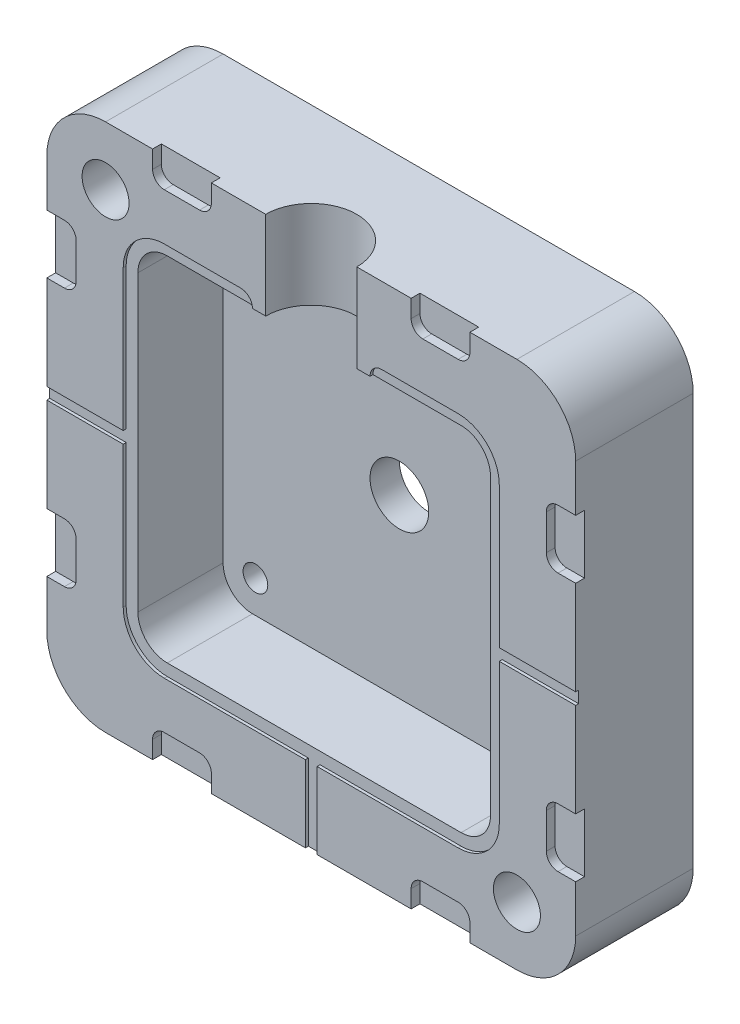
SolidWorks part; units mm, degrees
material "Alliage 1060"
ref_plane "Plan de face" through (0, 0, 0) normal (0, 0, 1) x (1, 0, 0)
ref_plane "Plan de dessus" through (0, 0, 0) normal (0, 1, 0) x (1, 0, 0)
ref_plane "Plan de droite" through (0, 0, 0) normal (1, 0, 0) x (0, 0, -1)
sketch "Esquisse1" plane through (0, 0, 0) normal (0, 0, 1) x (1, 0, 0)
  line L1 (-45, -45) -> (45, -45)
  line L2 (-45, -45) -> (-45, 45)
  line L3 (-45, 45) -> (45, 45)
  line L4 (45, -45) -> (45, 45)
  line L5 (-45, -45) -> (45, 45) construction
  line L6 (-45, 45) -> (45, -45) construction
  point P0 (0, 0)
  dimension "D1" = 90
  dimension "D2" = 90
extrude "Boss.-Extru.1" add sketch "Esquisse1" along normal blind 20
sketch "Esquisse2" plane through (0, 0, 20) normal (0, 0, 1) x (1, 0, 0)
  line L1 (-25, -30) -> (25, -30)
  line L2 (-30, -25) -> (-30, 25)
  line L3 (-25, 30) -> (25, 30)
  line L4 (30, -25) -> (30, 25)
  line L5 (-30, -30) -> (30, 30) construction
  line L6 (-30, 30) -> (30, -30) construction
  arc A0 (-25, -30) -> (-30, -25) centre (-25, -25) cw
  arc A1 (25, -30) -> (30, -25) centre (25, -25) ccw
  arc A2 (25, 30) -> (30, 25) centre (25, 25) cw
  arc A3 (-30, 25) -> (-25, 30) centre (-25, 25) cw
  point P0 (0, 0)
  dimension "D1" = 5
  dimension "D2" = 60
  dimension "D3" = 60
extrude "Enlèv. mat.-Extru.1" cut sketch "Esquisse2" against normal blind 15
sketch "Esquisse3" plane through (0, 0, 20) normal (0, 0, 1) x (1, 0, 0)
  line L0 (25, 32) -> (-25, 32)
  line L1 (-32, 25) -> (-32, -25)
  line L2 (-25, -32) -> (25, -32)
  line L3 (32, -25) -> (32, 25)
  line L4 (-25, -30) -> (25, -30)
  line L5 (30, -25) -> (30, 25)
  line L6 (25, 30) -> (-25, 30)
  line L7 (-30, 25) -> (-30, -25)
  line L8 (-25, -30) -> (25, -30)
  line L9 (30, -25) -> (30, 25)
  line L10 (25, 30) -> (-25, 30)
  line L11 (-30, 25) -> (-30, -25)
  line L12 (45, -45) -> (45, 45) construction
  line L13 (32, 1) -> (45, 1)
  line L14 (32, 1) -> (32, -1)
  line L15 (32, -1) -> (45, -1)
  line L16 (45, 1) -> (45, -1)
  line L17 (-45, 45) -> (-45, -45) construction
  line L18 (-32, 1) -> (-45, 1)
  line L19 (-32, 1) -> (-32, -1)
  line L20 (-32, -1) -> (-45, -1)
  line L21 (-45, 1) -> (-45, -1)
  line L22 (-45, -45) -> (45, -45) construction
  line L23 (1, -32) -> (-1, -32)
  line L24 (1, -32) -> (1, -45)
  line L25 (1, -45) -> (-1, -45)
  line L26 (-1, -32) -> (-1, -45)
  line L27 (0, -32) -> (0, 0) construction
  line L28 (-32, 0) -> (0, 0) construction
  line L29 (-10, 32) -> (-10, 30)
  line L30 (10, 32) -> (10, 30)
  arc A0 (-25, 32) -> (-32, 25) centre (-25, 25) ccw
  arc A1 (-32, -25) -> (-25, -32) centre (-25, -25) ccw
  arc A2 (25, -32) -> (32, -25) centre (25, -25) ccw
  arc A3 (32, 25) -> (25, 32) centre (25, 25) ccw
  arc A4 (-30, -25) -> (-25, -30) centre (-25, -25) ccw
  arc A5 (25, -30) -> (30, -25) centre (25, -25) ccw
  arc A6 (30, 25) -> (25, 30) centre (25, 25) ccw
  arc A7 (-25, 30) -> (-30, 25) centre (-25, 25) ccw
  arc A8 (-30, -25) -> (-25, -30) centre (-25, -25) ccw
  arc A9 (25, -30) -> (30, -25) centre (25, -25) ccw
  arc A10 (30, 25) -> (25, 30) centre (25, 25) ccw
  arc A11 (-25, 30) -> (-30, 25) centre (-25, 25) ccw
  circle A12 centre (-12, 30) radius 2
  circle A13 centre (12, 30) radius 2
  line M29 (25, -30) -> (-25, -30)
  arc M30 (-25, -30) -> (-30, -25) centre (-25, -25) cw
  line M31 (-30, -25) -> (-30, 25)
  arc M32 (-30, 25) -> (-25, 30) centre (-25, 25) cw
  line M33 (-25, 30) -> (25, 30)
  arc M34 (25, 30) -> (30, 25) centre (25, 25) cw
  line M35 (30, 25) -> (30, -25)
  arc M36 (30, -25) -> (25, -30) centre (25, -25) cw
  line M39 (-45, 45) -> (-45, -45)
  line M40 (-45, -45) -> (45, -45)
  dimension "D3" = 2
  dimension "D4" = 2
  dimension "D5" = 2
  dimension "D6" = 10
  dimension "D7" = 10
  dimension "D1" = 0
  dimension "D2" = 2
extrude "Enlèv. mat.-Extru.2" cut sketch "Esquisse3" against normal blind 0.5 contours L20 L1 L18 M39 | L2 L26 L24 M40 | L3 A3 L0 L30 L29 A0 L1 A1 L2 A2 M33 M34 M35 M36 M29 M30 M31 M32 | L10 A12 | A13 M33 | L15 L16 L13 L14
sketch "Esquisse4" plane through (0, 45, 0) normal (0, 1, 0) x (1, 0, 0)
  line L0 (45, -20) -> (-45, -20) construction
  circle A0 centre (0, -20) radius 7.75
  dimension "D1" = 15.5
fillet "Congé1" radius 10 4 edges at (-45, -45, 10) (45, -45, 10) (-45, 45, 10) (45, 45, 10)
sketch "Esquisse6" plane through (0, 0, 20) normal (0, 0, 1) x (1, 0, 0)
  circle A0 centre (-35, 35) radius 4
  circle A1 centre (35, -35) radius 4
  dimension "D1" = 8
  dimension "D2" = 8
  dimension "D3" = 35
  dimension "D4" = 35
  dimension "D5" = 35
  dimension "D6" = 35
extrude "Enlèv. mat.-Extru.4" cut sketch "Esquisse6" against normal through all
sketch "Esquisse7" plane through (0, 0, 5) normal (0, 0, 1) x (1, 0, 0)
  circle A0 centre (0, 0) radius 5
  dimension "D1" = 10
extrude "Enlèv. mat.-Extru.5" cut sketch "Esquisse7" against normal through all
sketch "Esquisse8" plane through (0, 0, 20) normal (0, 0, 1) x (1, 0, 0)
  line L0 (35, 45) -> (-35, 45) construction
  line L1 (-27, 45) -> (-17, 45)
  line L2 (-27, 45) -> (-27, 42)
  line L3 (-25, 40) -> (-19, 40)
  line L4 (-17, 45) -> (-17, 42)
  line L5 (35, 45) -> (-35, 45) construction
  line L6 (17, 45) -> (27, 45)
  line L7 (17, 45) -> (17, 42)
  line L8 (19, 40) -> (25, 40)
  line L9 (27, 45) -> (27, 42)
  line L10 (45, 27) -> (42, 27)
  line L11 (40, 25) -> (40, 19)
  line L12 (45, 17) -> (42, 17)
  line L13 (45, 27) -> (45, 17)
  line L14 (45, -17) -> (42, -17)
  line L15 (45, -17) -> (45, -27)
  line L16 (45, -27) -> (42, -27)
  line L17 (40, -19) -> (40, -25)
  line L18 (27, -45) -> (27, -42)
  line L19 (25, -40) -> (19, -40)
  line L20 (17, -45) -> (17, -42)
  line L21 (27, -45) -> (17, -45)
  line L22 (-17, -45) -> (-17, -42)
  line L23 (-17, -45) -> (-27, -45)
  line L24 (-27, -45) -> (-27, -42)
  line L25 (-19, -40) -> (-25, -40)
  line L26 (-45, -27) -> (-42, -27)
  line L27 (-40, -25) -> (-40, -19)
  line L28 (-45, -17) -> (-42, -17)
  line L29 (-45, -27) -> (-45, -17)
  line L30 (-45, 17) -> (-42, 17)
  line L31 (-45, 17) -> (-45, 27)
  line L32 (-45, 27) -> (-42, 27)
  line L33 (-40, 19) -> (-40, 25)
  arc A0 (27, 42) -> (25, 40) centre (25, 42) cw
  arc A1 (19, 40) -> (17, 42) centre (19, 42) cw
  arc A2 (-17, 42) -> (-19, 40) centre (-19, 42) cw
  arc A3 (-25, 40) -> (-27, 42) centre (-25, 42) cw
  arc A4 (40, 25) -> (42, 27) centre (42, 25) cw
  arc A5 (42, 17) -> (40, 19) centre (42, 19) cw
  arc A6 (40, -19) -> (42, -17) centre (42, -19) cw
  arc A7 (42, -27) -> (40, -25) centre (42, -25) cw
  arc A8 (25, -40) -> (27, -42) centre (25, -42) cw
  arc A9 (17, -42) -> (19, -40) centre (19, -42) cw
  arc A10 (-19, -40) -> (-17, -42) centre (-19, -42) cw
  arc A11 (-27, -42) -> (-25, -40) centre (-25, -42) cw
  arc A12 (-40, -25) -> (-42, -27) centre (-42, -25) cw
  arc A13 (-42, -17) -> (-40, -19) centre (-42, -19) cw
  arc A14 (-40, 19) -> (-42, 17) centre (-42, 19) cw
  arc A15 (-42, 27) -> (-40, 25) centre (-42, 25) cw
  point P15 (27, 40)
  point P18 (17, 40)
  point P21 (-17, 40)
  point P24 (-27, 40)
  point P76 (0, 0)
  dimension "D6" = 2
  dimension "D1" = 10
  dimension "D2" = 10
  dimension "D3" = 17
  dimension "D4" = 17
  dimension "D5" = 5
  dimension "D7" = 4
extrude "Enlèv. mat.-Extru.6" cut sketch "Esquisse8" against normal blind 1.5
sketch "Esquisse9" plane through (0, 0, 5) normal (0, 0, 1) x (1, 0, 0)
  line L0 (30, -25) -> (30, 25) construction
  line L1 (-24.5, -24.5) -> (24.5, -24.5) construction
  line L2 (-24.5, -24.5) -> (-24.5, 24.5) construction
  line L3 (-24.5, 24.5) -> (24.5, 24.5) construction
  line L4 (24.5, -24.5) -> (24.5, 24.5) construction
  line L5 (-24.5, -24.5) -> (24.5, 24.5) construction
  line L6 (-24.5, 24.5) -> (24.5, -24.5) construction
  line L7 (25, 30) -> (-25, 30) construction
  point P0 (0, 0)
  dimension "D1" = 5.5
  dimension "D2" = 5.5
hole_wizard "Trou taraudé M51" positions "Esquisse3D1" profile "Esquisse10" tap size "M5" standard "ISO"
sketch3d "Esquisse3D1"
  point P0 (-24.5, 24.5, 5)
  point P3 (24.5, 24.5, 5)
  point P6 (24.5, -24.5, 5)
  point P9 (-24.5, -24.5, 5)
sketch "Esquisse10" plane through (-24.5, 24.5, 5) normal (1, 0, 0) x (0, -1, 0)
  line L0 (0, 0) -> (0, 15.2618)
  line L1 (0, 15.2618) -> (2.1, 14)
  line L2 (2.1, 14) -> (2.1, 0)
  line L5 (2.1, 0) -> (0, 0)
  line L10 (0, 15.2618) -> (-2.1, 14) construction
  line L11 (0, -6.35) -> (0, 107.95) construction
  dimension "Diamètre du trou pour taraudage" = 4.2
  dimension "Profondeur du trou pour taraudage" = 14
  dimension "Angle de pointe" = 118
cosmetic thread "Filetage de perçage1" parameters "D1"=5, "D2"=5
cosmetic thread "Filetage de perçage2" parameters "D1"=5, "D2"=5
cosmetic thread "Filetage de perçage3" parameters "D1"=5, "D2"=5
cosmetic thread "Filetage de perçage4" parameters "D1"=5, "D2"=5
extrude "Enlèv. mat.-Extru.7" cut sketch "Esquisse4" against normal up to next contours A0
